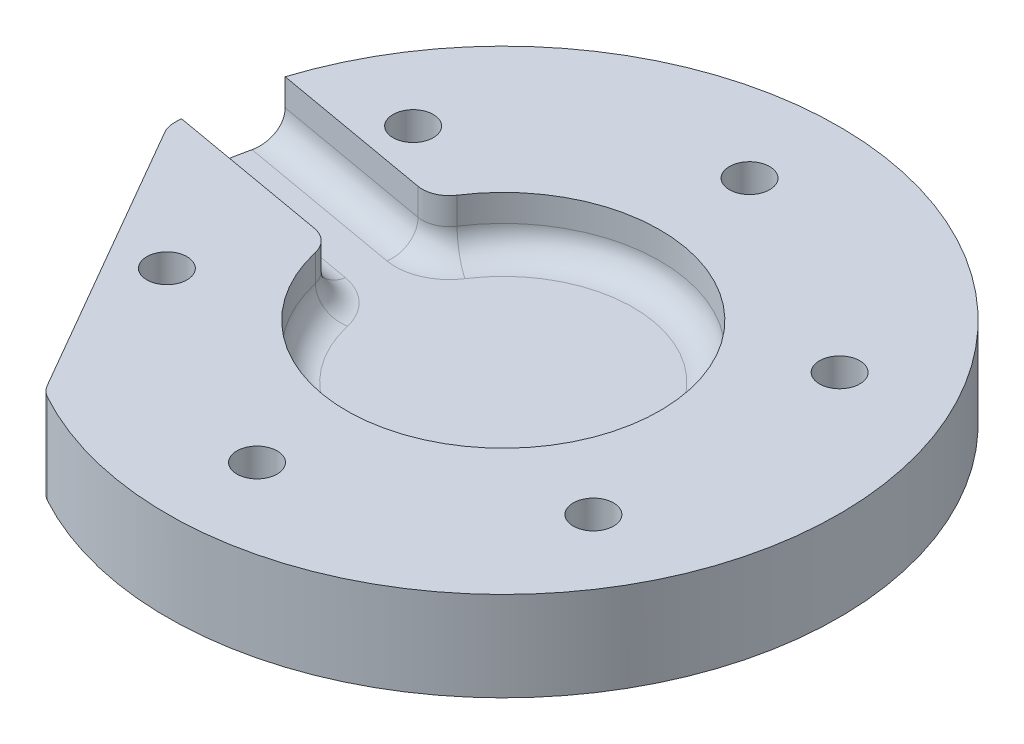
SolidWorks part; units mm, degrees
ref_plane "Front" through (0, 0, 0) normal (0, 0, 1) x (1, 0, 0)
ref_plane "Top" through (0, 0, 0) normal (0, 1, 0) x (1, 0, 0)
ref_plane "Right" through (0, 0, 0) normal (1, 0, 0) x (0, 0, -1)
sketch "Sketch1" plane through (0, 0, 0) normal (0, 1, 0) x (1, 0, 0)
  circle A0 centre (0, 0) radius 37.5
  circle A1 centre (0, 27.5) radius 2.25
  circle A2 centre (23.8157, 13.75) radius 2.25
  circle A3 centre (23.8157, -13.75) radius 2.25
  circle A4 centre (0, -27.5) radius 2.25
  circle A5 centre (-23.8157, -13.75) radius 2.25
  circle A6 centre (-23.8157, 13.75) radius 2.25
  point P18 (0, 0)
  dimension "D1" = 75
  dimension "D2" = 4.5
  dimension "D3" = 27.5
  dimension "D5" = 13.75
  dimension "D4" = 6
  dimension "D6" = 23.8157
  dimension "D7" = 60
extrude "Boss-Extrude1" add sketch "Sketch1" along normal blind 10
sketch "Sketch4" plane through (0, 10, 0) normal (0, 1, 0) x (1, 0, 0)
  circle A0 centre (0, 0) radius 17.5
  dimension "D1" = 35
extrude "Cut-Extrude3" cut sketch "Sketch4" against normal blind 6
sketch "Sketch2" plane through (0, 10, 0) normal (0, 1, 0) x (1, 0, 0)
  line L0 (12.1851, 0) -> (10.8382, -7.6388)
  line L1 (0, 0) -> (12.1851, 0) construction
  line L2 (12.6859, 2.8403) -> (-35.7323, 11.3777)
  line L3 (10.9495, -7.0078) -> (-37.4688, 1.5296)
  line L4 (12.1851, 0) -> (12.6859, 2.8403)
  circle A1 centre (0, 0) radius 37.5 construction
  circle A2 centre (0, 0) radius 37.5
  dimension "D1" = 80
  dimension "D2" = 5
  dimension "D3" = 5
  dimension "D4" = 12
  dimension "D5" = 10
extrude "Cut-Extrude1" cut sketch "Sketch2" against normal blind 6
sketch "Sketch3" plane through (0, 0, 0) normal (0, -1, 0) x (1, 0, 0)
  line L1 (-18.75, 32.476) -> (-37.5, 0)
  line L2 (-37.5, 0) -> (-18.75, -32.476)
  line L3 (-18.75, -32.476) -> (18.75, -32.476)
  line L4 (18.75, -32.476) -> (37.5, 0)
  line L5 (37.5, 0) -> (18.75, 32.476)
  line L6 (18.75, 32.476) -> (-18.75, 32.476)
  circle A0 centre (0, 0) radius 37.5
  circle A1 centre (0, 0) radius 32.476 construction
  circle A2 centre (0, 0) radius 37.5 construction
  point P12 (0, 0)
  circle M5 centre (0, 0) radius 37.5
extrude "Cut-Extrude2" cut sketch "Sketch3" against normal blind 10 contours L1 M5
fillet "Fillet1" radius 3 7 edges at (-37.5, 5, 0) (-18.75, 5, 32.476) (-17.384, 7, 2.0119) (-15.6475, 7, -7.8362) (17.2341, 4, 3.0388) (-25.6899, 4, -9.607) (-27.4264, 4, 0.2411)
